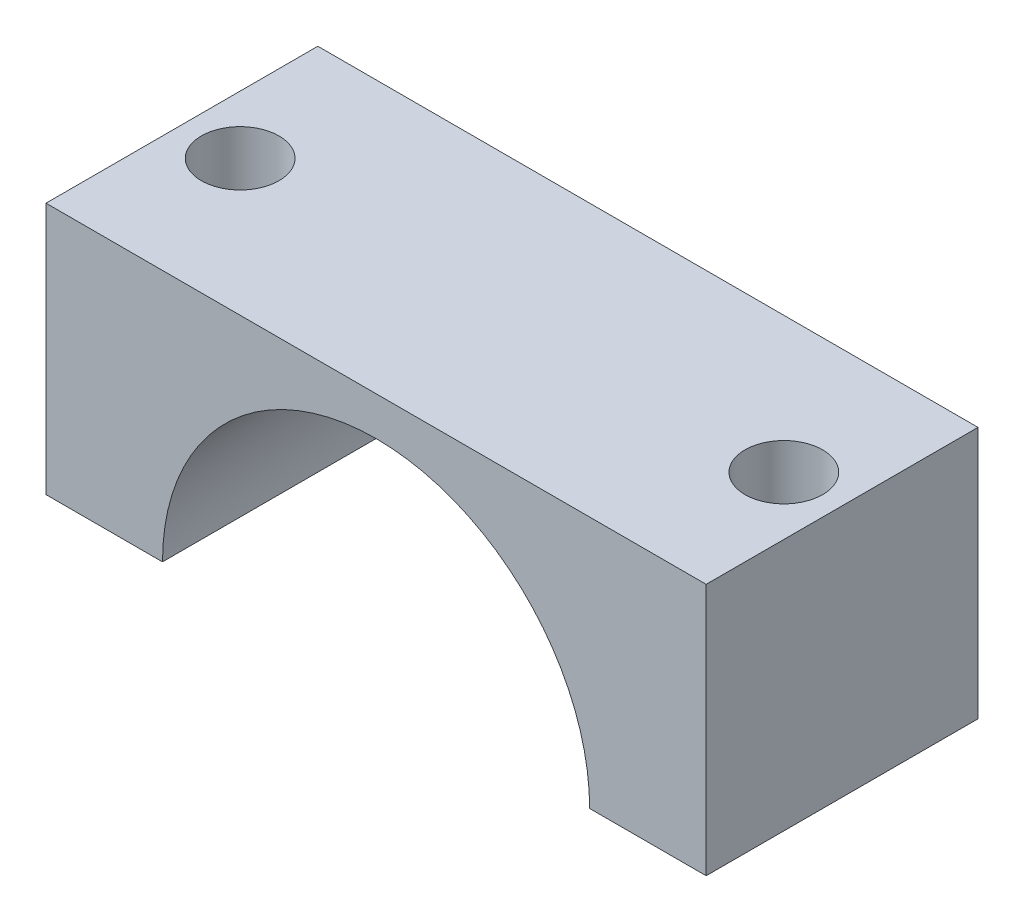
SolidWorks part; units mm, degrees
ref_plane "Plan de face" through (0, 0, 0) normal (0, 0, 1) x (1, 0, 0)
ref_plane "Plan de dessus" through (0, 0, 0) normal (0, 1, 0) x (1, 0, 0)
ref_plane "Plan de droite" through (0, 0, 0) normal (1, 0, 0) x (0, 0, -1)
sketch "Esquisse1" plane through (0, 0, 0) normal (0, 0, 1) x (1, 0, 0)
  line L0 (-17, 0) -> (-17, 13)
  line L1 (17, 0) -> (17, 13)
  line L2 (0, 0) -> (0, 14.5849) construction
  line L4 (-17, 0) -> (-11, 0)
  line L5 (11, 0) -> (17, 0)
  line L6 (-17, 13) -> (17, 13)
  arc A0 (11, 0) -> (-11, 0) centre (0, 0) ccw
extrude "Extrusion1" add sketch "Esquisse1" along normal blind 14
sketch "Esquisse2" plane through (0, 13, 0) normal (0, 1, 0) x (1, 0, 0)
  circle A0 centre (-14, -7) radius 2
  circle A1 centre (14, -7) radius 2
extrude "Extrusion2" cut sketch "Esquisse2" against normal through all
